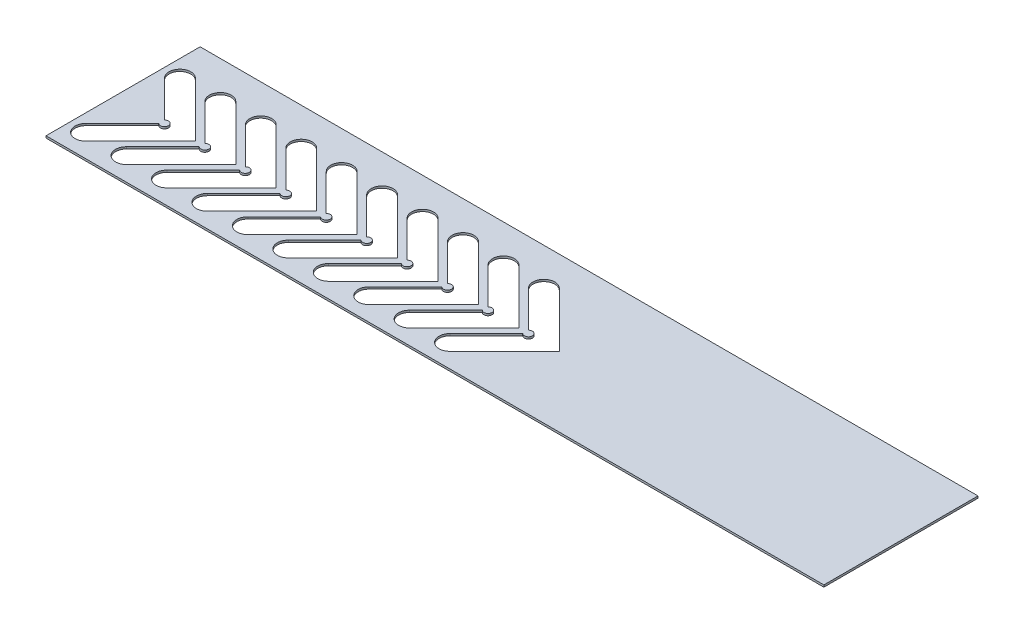
SolidWorks part; units mm, degrees
ref_plane "Front Plane" through (0, 0, 0) normal (0, 0, 1) x (1, 0, 0)
ref_plane "Top Plane" through (0, 0, 0) normal (0, 1, 0) x (1, 0, 0)
ref_plane "Right Plane" through (0, 0, 0) normal (1, 0, 0) x (0, 0, -1)
sketch "Sketch1" plane through (0, 0, 0) normal (0, 1, 0) x (1, 0, 0)
  line L0 (0, 0) -> (-28.0472, 0) construction
  line L1 (-20.0821, -17.3038) -> (172.2544, -17.3038)
  line L2 (-20.0821, -17.3038) -> (-20.0821, 20.8038)
  line L3 (-20.0821, 20.8038) -> (172.2544, 20.8038)
  line L4 (172.2544, -17.3038) -> (172.2544, 20.8038)
  line L5 (-17.7913, 9.6946) -> (-8.8038, 0.7071)
  line L6 (-8.8038, -0.7071) -> (-17.7913, -9.6946)
  line L7 (-13.9729, 13.513) -> (-0.4599, 0)
  line L8 (-0.4599, 0) -> (-13.9729, -13.513)
  line L9 (-15.8821, 11.6038) -> (-15.8821, -11.6038) construction
  line L10 (-3.9729, 13.513) -> (9.5401, 0)
  line L11 (-17.7913, 9.6946) -> (-8.0967, 0) construction
  line L12 (-8.0967, 0) -> (-17.7913, -9.6946) construction
  line L13 (9.5401, 0) -> (-3.9729, -13.513)
  line L14 (1.1962, -0.7071) -> (-7.7913, -9.6946)
  line L15 (-7.7913, 9.6946) -> (1.1962, 0.7071)
  line L16 (6.0271, 13.513) -> (19.5401, 0)
  line L17 (19.5401, 0) -> (6.0271, -13.513)
  line L18 (11.1962, -0.7071) -> (2.2087, -9.6946)
  line L19 (2.2087, 9.6946) -> (11.1962, 0.7071)
  line L20 (16.0271, 13.513) -> (29.5401, 0)
  line L21 (29.5401, 0) -> (16.0271, -13.513)
  line L22 (21.1962, -0.7071) -> (12.2087, -9.6946)
  line L23 (12.2087, 9.6946) -> (21.1962, 0.7071)
  line L24 (26.0271, 13.513) -> (39.5401, 0)
  line L25 (39.5401, 0) -> (26.0271, -13.513)
  line L26 (31.1962, -0.7071) -> (22.2087, -9.6946)
  line L27 (22.2087, 9.6946) -> (31.1962, 0.7071)
  line L28 (36.0271, 13.513) -> (49.5401, 0)
  line L29 (49.5401, 0) -> (36.0271, -13.513)
  line L30 (41.1962, -0.7071) -> (32.2087, -9.6946)
  line L31 (32.2087, 9.6946) -> (41.1962, 0.7071)
  line L32 (46.0271, 13.513) -> (59.5401, 0)
  line L33 (59.5401, 0) -> (46.0271, -13.513)
  line L34 (51.1962, -0.7071) -> (42.2087, -9.6946)
  line L35 (42.2087, 9.6946) -> (51.1962, 0.7071)
  line L36 (56.0271, 13.513) -> (69.5401, 0)
  line L37 (69.5401, 0) -> (56.0271, -13.513)
  line L38 (61.1962, -0.7071) -> (52.2087, -9.6946)
  line L39 (52.2087, 9.6946) -> (61.1962, 0.7071)
  line L40 (66.0271, 13.513) -> (79.5401, 0)
  line L41 (79.5401, 0) -> (66.0271, -13.513)
  line L42 (71.1962, -0.7071) -> (62.2087, -9.6946)
  line L43 (62.2087, 9.6946) -> (71.1962, 0.7071)
  line L44 (76.0271, 13.513) -> (89.5401, 0)
  line L45 (89.5401, 0) -> (76.0271, -13.513)
  line L46 (81.1962, -0.7071) -> (72.2087, -9.6946)
  line L47 (72.2087, 9.6946) -> (81.1962, 0.7071)
  line L48 (-18.5821, 14.3038) -> (-13.9729, 14.3038) construction
  line L49 (-18.5821, 14.3038) -> (-18.5821, 8.5066) construction
  line L50 (-18.5821, -14.3038) -> (-13.9729, -14.3038) construction
  arc A0 (-17.7913, 9.6946) -> (-13.9729, 13.513) centre (-15.8821, 11.6038) cw
  arc A1 (-17.7913, -9.6946) -> (-13.9729, -13.513) centre (-15.8821, -11.6038) ccw
  arc A2 (-8.8038, -0.7071) -> (-8.8038, 0.7071) centre (-8.0967, 0) ccw
  arc A3 (-7.7913, -9.6946) -> (-3.9729, -13.513) centre (-5.8821, -11.6038) ccw
  arc A4 (1.1962, -0.7071) -> (1.1962, 0.7071) centre (1.9033, 0) ccw
  arc A5 (-7.7913, 9.6946) -> (-3.9729, 13.513) centre (-5.8821, 11.6038) cw
  arc A6 (2.2087, -9.6946) -> (6.0271, -13.513) centre (4.1179, -11.6038) ccw
  arc A7 (11.1962, -0.7071) -> (11.1962, 0.7071) centre (11.9033, 0) ccw
  arc A8 (2.2087, 9.6946) -> (6.0271, 13.513) centre (4.1179, 11.6038) cw
  arc A9 (12.2087, -9.6946) -> (16.0271, -13.513) centre (14.1179, -11.6038) ccw
  arc A10 (21.1962, -0.7071) -> (21.1962, 0.7071) centre (21.9033, 0) ccw
  arc A11 (12.2087, 9.6946) -> (16.0271, 13.513) centre (14.1179, 11.6038) cw
  arc A12 (22.2087, -9.6946) -> (26.0271, -13.513) centre (24.1179, -11.6038) ccw
  arc A13 (31.1962, -0.7071) -> (31.1962, 0.7071) centre (31.9033, 0) ccw
  arc A14 (22.2087, 9.6946) -> (26.0271, 13.513) centre (24.1179, 11.6038) cw
  arc A15 (32.2087, -9.6946) -> (36.0271, -13.513) centre (34.1179, -11.6038) ccw
  arc A16 (41.1962, -0.7071) -> (41.1962, 0.7071) centre (41.9033, 0) ccw
  arc A17 (32.2087, 9.6946) -> (36.0271, 13.513) centre (34.1179, 11.6038) cw
  arc A18 (42.2087, -9.6946) -> (46.0271, -13.513) centre (44.1179, -11.6038) ccw
  arc A19 (51.1962, -0.7071) -> (51.1962, 0.7071) centre (51.9033, 0) ccw
  arc A20 (42.2087, 9.6946) -> (46.0271, 13.513) centre (44.1179, 11.6038) cw
  arc A21 (52.2087, -9.6946) -> (56.0271, -13.513) centre (54.1179, -11.6038) ccw
  arc A22 (61.1962, -0.7071) -> (61.1962, 0.7071) centre (61.9033, 0) ccw
  arc A23 (52.2087, 9.6946) -> (56.0271, 13.513) centre (54.1179, 11.6038) cw
  arc A24 (62.2087, -9.6946) -> (66.0271, -13.513) centre (64.1179, -11.6038) ccw
  arc A25 (71.1962, -0.7071) -> (71.1962, 0.7071) centre (71.9033, 0) ccw
  arc A26 (62.2087, 9.6946) -> (66.0271, 13.513) centre (64.1179, 11.6038) cw
  arc A27 (72.2087, -9.6946) -> (76.0271, -13.513) centre (74.1179, -11.6038) ccw
  arc A28 (81.1962, -0.7071) -> (81.1962, 0.7071) centre (81.9033, 0) ccw
  arc A29 (72.2087, 9.6946) -> (76.0271, 13.513) centre (74.1179, 11.6038) cw
  point P112 (0, 0)
  dimension "D2" = 19.3
  dimension "D4" = 1
  dimension "D1" = 2.7
  dimension "D3" = 19.3
  dimension "D5" = 6.5
  dimension "D6" = 3
  dimension "D7" = 1.5
extrude "Boss-Extrude1" add sketch "Sketch1" along normal blind 0.5
